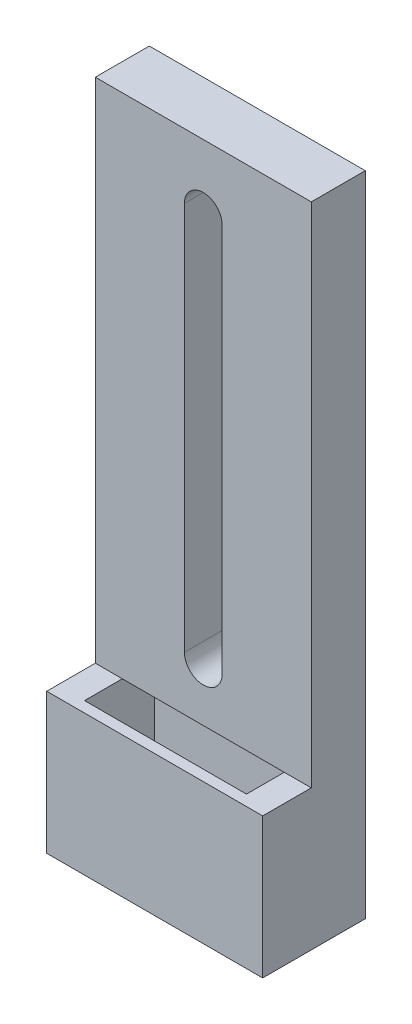
SolidWorks part; units mm, degrees
material "ABS PC"
ref_plane "Front Plane" through (0, 0, 0) normal (0, 0, 1) x (1, 0, 0)
ref_plane "Top Plane" through (0, 0, 0) normal (0, 1, 0) x (1, 0, 0)
ref_plane "Right Plane" through (0, 0, 0) normal (1, 0, 0) x (0, 0, -1)
sketch "Sketch1" plane through (0, 0, 0) normal (0, 0, 1) x (1, 0, 0)
  line L0 (0, 0) -> (0, 60)
  line L1 (0, 0) -> (20, 0)
  line L2 (0, 60) -> (20, 60)
  line L3 (20, 0) -> (20, 60)
  dimension "D1" = 60
  dimension "D2" = 20
extrude "Boss-Extrude1" add sketch "Sketch1" along normal blind 5
sketch "Sketch2" plane through (0, 0, 5) normal (0, 0, 1) x (1, 0, 0)
  line L0 (0, 0) -> (20, 0)
  line L1 (0, 0) -> (0, 13)
  line L2 (20, 0) -> (20, 13)
  line L3 (0, 13) -> (20, 13)
  dimension "D1" = 13
extrude "Boss-Extrude2" add sketch "Sketch2" along normal blind 4.5
sketch "Sketch3" plane through (0, 13, 0) normal (0, 1, 0) x (1, 0, 0)
  line L0 (17.5, -2) -> (17.5, -8.5)
  line L1 (17.5, -2) -> (2.5, -2)
  line L2 (17.5, -8.5) -> (2.5, -8.5)
  line L3 (2.5, -2) -> (2.5, -8.5)
  line L5 (0, -9.5) -> (0, -5) construction
  line L6 (20, -9.5) -> (0, -9.5) construction
  dimension "D1" = 15
  dimension "D2" = 6.5
  dimension "D3" = 2.5
  dimension "D4" = 1
extrude "Cut-Extrude1" cut sketch "Sketch3" against normal through all
sketch "Sketch4" plane through (0, 0, 5) normal (0, 0, 1) x (1, 0, 0)
  line L0 (10, 54) -> (10, 18) construction
  line L1 (11.75, 54) -> (11.75, 18)
  line L2 (8.25, 54) -> (8.25, 18)
  line L3 (20, 60) -> (0, 60) construction
  line L4 (20, 13) -> (20, 60) construction
  arc A0 (11.75, 54) -> (8.25, 54) centre (10, 54) ccw
  arc A1 (8.25, 18) -> (11.75, 18) centre (10, 18) ccw
  point P2 (10, 36)
  dimension "D1" = 3.5
  dimension "D2" = 6
  dimension "D3" = 36
  dimension "D4" = 10
extrude "Cut-Extrude2" cut sketch "Sketch4" against normal blind 10
